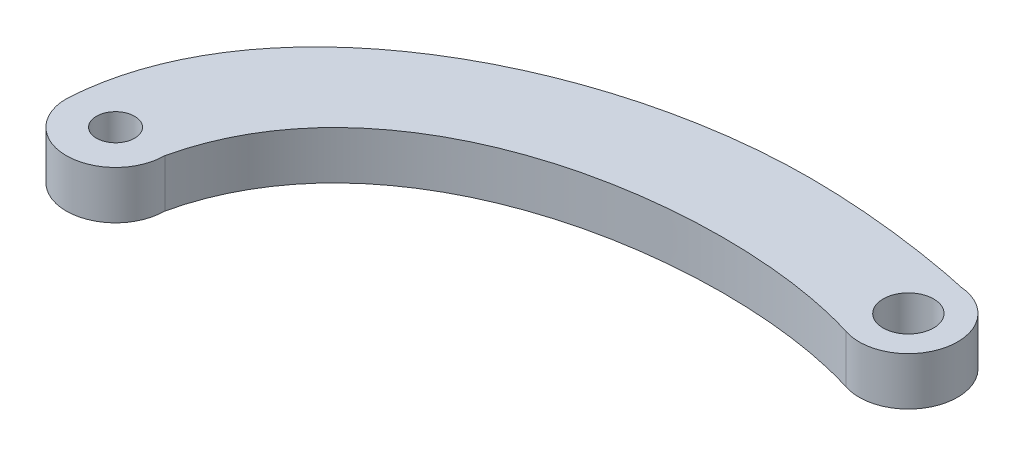
SolidWorks part; units mm, degrees
ref_plane "Front Plane" through (0, 0, 0) normal (0, 0, 1) x (1, 0, 0)
ref_plane "Top Plane" through (0, 0, 0) normal (0, 1, 0) x (1, 0, 0)
ref_plane "Right Plane" through (0, 0, 0) normal (1, 0, 0) x (0, 0, -1)
sketch "Sketch1" plane through (0, 0, 0) normal (0, 1, 0) x (1, 0, 0)
  arc A0 (-14.82, -5.2152) -> (-6.82, -5.2152) centre (-10.82, -5.2152) ccw
  circle A1 centre (-10.82, -5.2152) radius 1.55
  arc A2 (33.1813, 10.0994) -> (34.7962, 17.8712) centre (34.4762, 13.884) ccw
  circle A3 centre (34.4762, 13.884) radius 2.05
  spline S0 degree 3 poles (-14.82, -5.2152) (-14.0249, 9.6683) (10.7805, 22.9478) (33.5182, 18.1691) (34.7962, 17.8712) knots 0 0 0 0 0.692921 1 1 1 1
  spline S1 degree 3 poles (-6.82, -5.2152) (-3.1043, 11.2262) (20.3044, 14.0901) (33.1813, 10.0994) knots 0 0 0 0 1 1 1 1
  dimension "D1" = 8
  dimension "D2" = 3.1
  dimension "D3" = 8
  dimension "D4" = 4.1
extrude "Boss-Extrude1" add sketch "Sketch1" along normal blind 3.9
